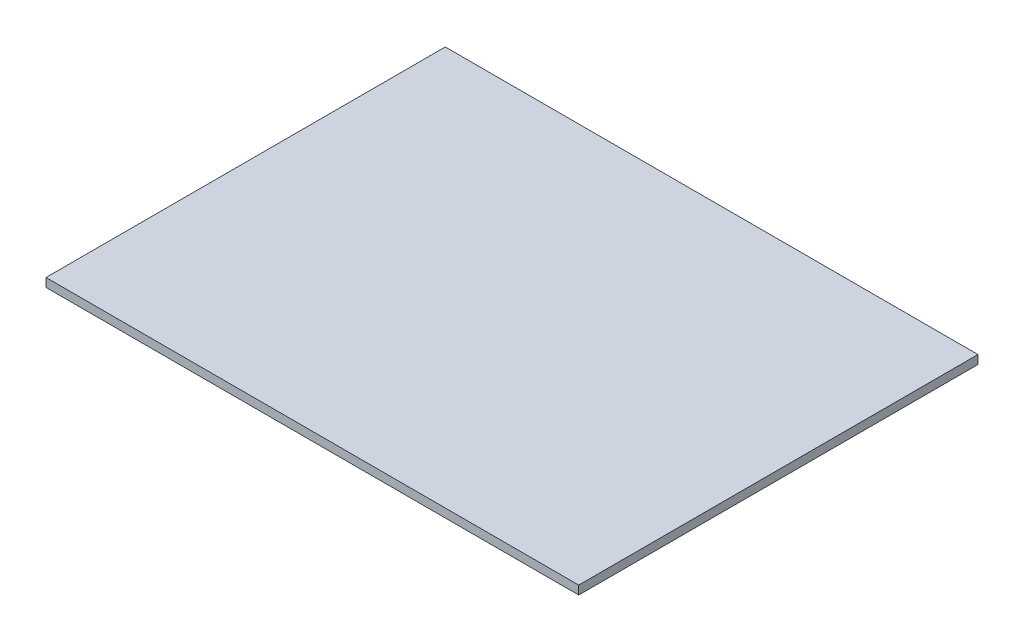
SolidWorks part; units mm, degrees
ref_plane "Front Plane" through (0, 0, 0) normal (0, 0, 1) x (1, 0, 0)
ref_plane "Top Plane" through (0, 0, 0) normal (0, 1, 0) x (1, 0, 0)
ref_plane "Right Plane" through (0, 0, 0) normal (1, 0, 0) x (0, 0, -1)
sketch "Sketch1" plane through (0, 0, 0) normal (0, 1, 0) x (1, 0, 0)
  line L1 (-2054.2838, 1678.2294) -> (1023.7162, 1678.2294)
  line L2 (-2054.2838, 1678.2294) -> (-2054.2838, -628.7706)
  line L3 (-2054.2838, -628.7706) -> (1023.7162, -628.7706)
  line L4 (1023.7162, 1678.2294) -> (1023.7162, -628.7706)
  dimension "D1" = 2307
  dimension "D2" = 3078
extrude "Boss-Extrude1" add sketch "Sketch1" along normal blind 50
